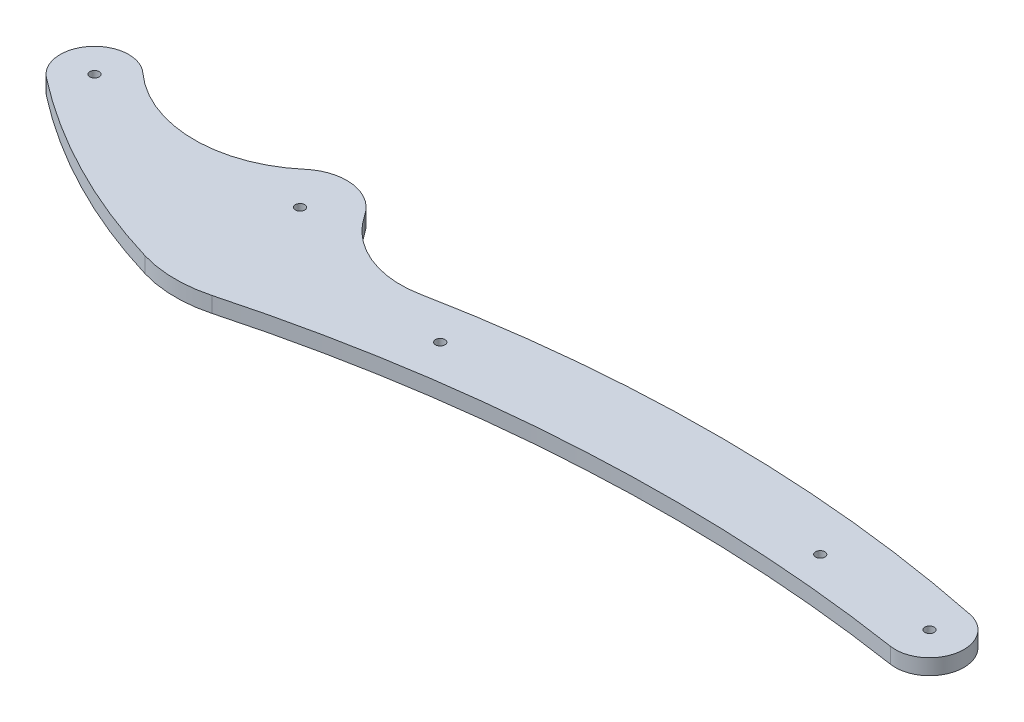
SolidWorks part; units mm, degrees
ref_plane "Front Plane" through (0, 0, 0) normal (0, 0, 1) x (1, 0, 0)
ref_plane "Top Plane" through (0, 0, 0) normal (0, 1, 0) x (1, 0, 0)
ref_plane "Right Plane" through (0, 0, 0) normal (1, 0, 0) x (0, 0, -1)
sketch "Sketch1" plane through (0, 0, 0) normal (0, 1, 0) x (1, 0, 0)
  line L0 (0, 0) -> (70, 0) construction
  line L1 (70, 0) -> (70, -4) construction
  line L2 (70, -4) -> (288.5, -4) construction
  line L3 (288.5, -4) -> (288.5, -20.4) construction
  line L4 (130, -4) -> (130, -19) construction
  line L5 (250, -4) -> (250, -17) construction
  circle A0 centre (0, 0) radius 1.5
  circle A1 centre (70, -4) radius 1.5
  arc A2 (7.3862, 8.1513) -> (-6.7476, -8.6873) centre (0, 0) ccw
  arc A3 (82.5615, 4.1982) -> (60.2487, 7.3979) centre (70, -4) ccw
  arc A4 (7.3862, 8.1513) -> (60.2487, 7.3979) centre (34.2453, 37.7923) ccw
  arc A5 (58.5159, -42.316) -> (80.4056, -42.6228) centre (70, -4) ccw
  arc A6 (-6.7476, -8.6873) -> (58.5159, -42.316) centre (115.9365, 149.2639) ccw
  arc A8 (82.5615, 4.1982) -> (113.4631, -8.8437) centre (107.6844, 20.5945) ccw
  circle A9 centre (288.5, -20.4) radius 1.5
  arc A10 (286.8204, -31.271) -> (288.5, -9.4) centre (288.5, -20.4) ccw
  arc A11 (286.8204, -31.271) -> (80.4056, -42.6228) centre (210.476, -525.4082) ccw
  arc A12 (290.7139, -9.6251) -> (113.4631, -8.8437) centre (200.1436, -450.4164) ccw
  arc A13 (30.2005, 0) -> (30.0507, -1.9871) centre (70, -4) ccw
  circle A14 centre (130, -19) radius 1.5
  circle A15 centre (250, -17) radius 1.5
  point P33 (225.8247, -17.4405)
  dimension "D1" = 3
  dimension "D4" = 3
  dimension "D5" = 22
  dimension "D6" = 30
  dimension "D7" = 40
  dimension "D8" = 40
  dimension "D9" = 200
  dimension "D10" = 30
  dimension "D11" = 218.5
  dimension "D13" = 3
  dimension "D14" = 22
  dimension "D15" = 500
  dimension "D16" = 450
  dimension "D17" = 15
  dimension "D18" = 3
  dimension "D21" = 3
  dimension "D2" = 70
  dimension "D3" = 4
  dimension "D12" = 16.4
  dimension "D19" = 60
  dimension "D20" = 13
  dimension "D22" = 120
extrude "Boss-Extrude1" add sketch "Sketch1" along normal blind 5
